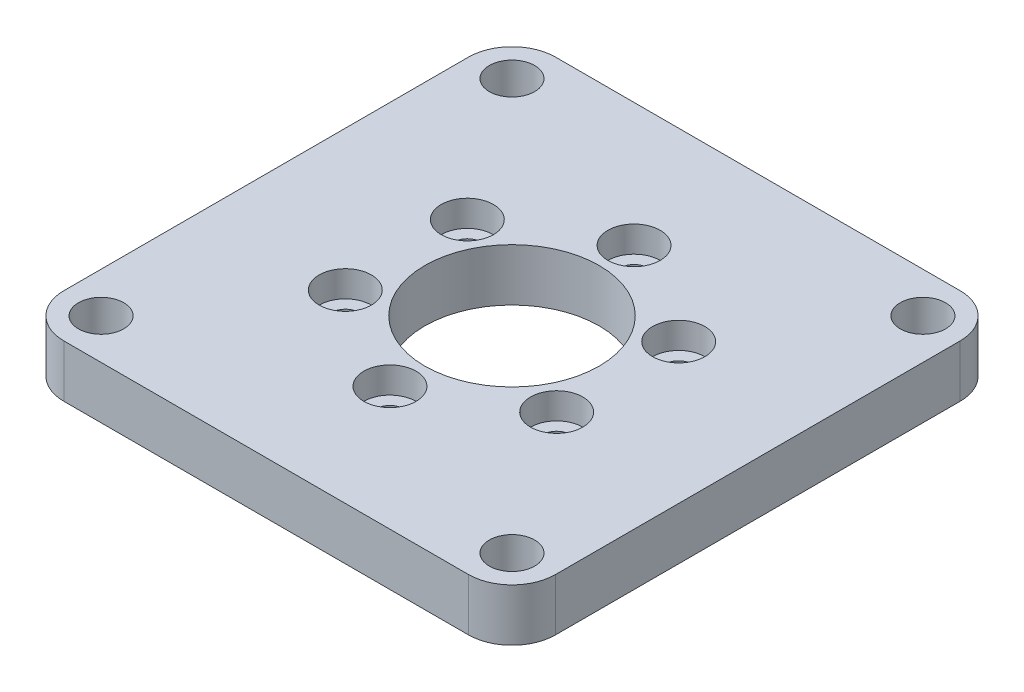
SolidWorks part; units mm, degrees
ref_plane "Front Plane" through (0, 0, 0) normal (0, 0, 1) x (1, 0, 0)
ref_plane "Top Plane" through (0, 0, 0) normal (0, 1, 0) x (1, 0, 0)
ref_plane "Right Plane" through (0, 0, 0) normal (1, 0, 0) x (0, 0, -1)
sketch "Sketch1" plane through (0, 0, 0) normal (0, 1, 0) x (1, 0, 0)
  line L1 (-28.2, 28.2) -> (28.2, 28.2)
  line L2 (-28.2, 28.2) -> (-28.2, -28.2)
  line L3 (-28.2, -28.2) -> (28.2, -28.2)
  line L4 (28.2, 28.2) -> (28.2, -28.2)
  line L5 (-28.2, 28.2) -> (28.2, -28.2) construction
  line L6 (-28.2, -28.2) -> (28.2, 28.2) construction
  point P0 (0, 0)
  dimension "D1" = 56.4
  dimension "D2" = 56.4
extrude "Boss-Extrude1" add sketch "Sketch1" along normal mid plane 6
fillet "Fillet1" radius 5 4 edges at (-28.2, 0, 28.2) (-28.2, 0, -28.2) (28.2, 0, -28.2) (28.2, 0, 28.2)
sketch "Sketch2" plane through (0, -3, 0) normal (0, -1, 0) x (1, 0, 0)
  line L1 (-23.57, -23.57) -> (23.57, -23.57) construction
  line L2 (-23.57, -23.57) -> (-23.57, 23.57) construction
  line L3 (-23.57, 23.57) -> (23.57, 23.57) construction
  line L4 (23.57, -23.57) -> (23.57, 23.57) construction
  line L5 (-23.57, -23.57) -> (23.57, 23.57) construction
  line L6 (-23.57, 23.57) -> (23.57, -23.57) construction
  circle A0 centre (-23.57, 23.57) radius 2.6
  circle A1 centre (23.57, 23.57) radius 2.6
  circle A2 centre (23.57, -23.57) radius 2.6
  circle A3 centre (-23.57, -23.57) radius 2.6
  point P0 (0, 0)
  dimension "D3" = 5.2
  dimension "D4" = 5.2
  dimension "D5" = 5.2
  dimension "D6" = 5.2
  dimension "D1" = 47.14
  dimension "D2" = 47.14
extrude "Cut-Extrude1" cut sketch "Sketch2" against normal through all
sketch "Sketch4" plane through (0, -3, 0) normal (0, -1, 0) x (1, 0, 0)
  circle A0 centre (0, 0) radius 10
  dimension "D1" = 20
extrude "Cut-Extrude3" cut sketch "Sketch4" against normal through all
sketch "Sketch5" plane through (0, 3, 0) normal (0, 1, 0) x (1, 0, 0)
  line L0 (0, 0) -> (0, 28.2) construction
  line L1 (23.2, 28.2) -> (-23.2, 28.2) construction
  circle A0 centre (0, 14) radius 1.55
  dimension "D1" = 3.1
  dimension "D2" = 14
extrude "Cut-Extrude4" cut sketch "Sketch5" against normal through all
sketch "Sketch6" plane through (0, 3, 0) normal (0, 1, 0) x (1, 0, 0)
  circle A0 centre (0, 14) radius 3
  dimension "D1" = 6
extrude "Cut-Extrude5" cut sketch "Sketch6" against normal blind 3
pattern_circular "CirPattern1" count 6 every 60 about axis through (0, 0, 0) along (0, 1, 0) of "Cut-Extrude4", "Cut-Extrude5"
